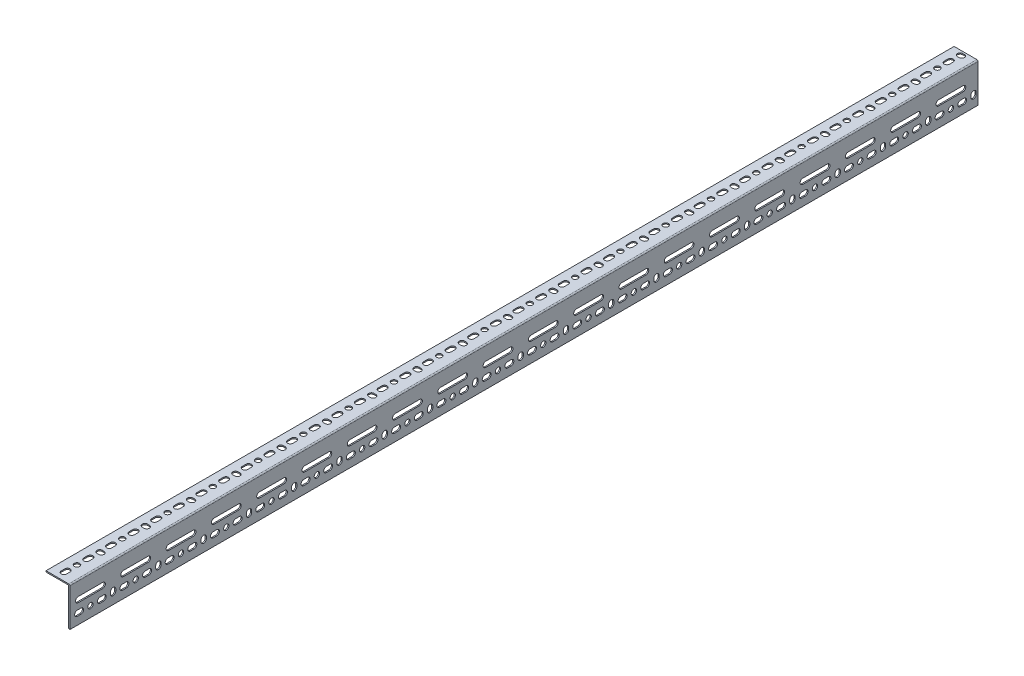
SolidWorks part; units mm, degrees
material "Black Iron Steel"
ref_plane "Front Plane" through (0, 0, 0) normal (0, 0, 1) x (1, 0, 0)
ref_plane "Top Plane" through (0, 0, 0) normal (0, 1, 0) x (1, 0, 0)
ref_plane "Right Plane" through (0, 0, 0) normal (1, 0, 0) x (0, 0, -1)
other "total length"
sketch "Sketch1" plane through (0, 0, 0) normal (0, 1, 0) x (1, 0, 0)
  line L0 (0, 0) -> (0, 1524)
  dimension "D1" = 1524
other "Structural Member1"
ref_plane "Plane1" through (0, 0, 0) normal (0, 0, 1) x (-1, 0, 0)
sketch "Sketch11" plane through (0, 0, 0) normal (0, 0, 1) x (-1, 0, 0)
  line L0 (0, 2) -> (0, 65.5)
  line L1 (0, 65.5) -> (1, 65.5)
  line L2 (2, 64.5) -> (2, 4)
  line L3 (4, 2) -> (39.1, 2)
  line L4 (40.1, 1) -> (40.1, 0)
  line L5 (40.1, 0) -> (2, 0)
  arc A0 (40.1, 1) -> (39.1, 2) centre (39.1, 1) ccw
  arc A1 (1, 65.5) -> (2, 64.5) centre (1, 64.5) cw
  arc A2 (4, 2) -> (2, 4) centre (4, 4) cw
  arc A3 (0, 2) -> (2, 0) centre (2, 2) ccw
  point P10 (21.05, 0)
  point P14 (0, 33.75)
  point P15 (2, 33.75)
  point P16 (21.05, 2)
  point P17 (2, 65.5)
  point P18 (40.1, 2)
  point P21 (0, 0)
  point P22 (0, 0)
  dimension "Radius_1" = 2
  dimension "D4" = 2
  dimension "D1" = 2
  dimension "H_leg" = 40.1
  dimension "D2" = 1
  dimension "D3" = 65.5
sketch "Sketch12" plane through (0, 0, 0) normal (0, 1, 0) x (1, 0, 0)
  line L0 (-22.6, 12.5) -> (-22.6, 18.5) construction
  line L1 (-27.1, 12.5) -> (-27.1, 18.5)
  line L2 (-18.1, 12.5) -> (-18.1, 18.5)
  line L3 (-40.1, 1524) -> (-40.1, 0) construction
  line L5 (-2, 0) -> (-40.1, 0) construction
  arc A0 (-27.1, 12.5) -> (-18.1, 12.5) centre (-22.6, 12.5) ccw
  arc A1 (-18.1, 18.5) -> (-27.1, 18.5) centre (-22.6, 18.5) ccw
  point P2 (-22.6, 15.5)
  dimension "D1" = 15
  dimension "D4" = 8
  dimension "D2" = 9
  dimension "D3" = 13
extrude "Slot 1.5" cut sketch "Sketch12" against normal through all
sketch "Sketch13" plane through (0, 0, 0) normal (0, 1, 0) x (1, 0, 0)
  line L0 (-22.6, 34.5) -> (-22.6, 15.5) construction
  circle A0 centre (-22.6, 34.5) radius 4.5
  arc A2 (-18.1, 18.5) -> (-27.1, 18.5) centre (-22.6, 18.5) ccw construction
  dimension "D1" = 7
  dimension "D2" = 9
extrude "Hole 1.5" cut sketch "Sketch13" against normal through all
sketch "Sketch18" plane through (0, 0, 0) normal (0, 1, 0) x (1, 0, 0)
  line L0 (-22.6, 72.5) -> (-19.6, 72.5) construction
  line L1 (-22.6, 77) -> (-19.6, 77)
  line L2 (-22.6, 68) -> (-19.6, 68)
  arc A0 (-22.6, 77) -> (-22.6, 68) centre (-22.6, 72.5) ccw
  arc A1 (-19.6, 68) -> (-19.6, 77) centre (-19.6, 72.5) ccw
  point P2 (-21.1, 72.5)
  dimension "D2" = 12
  dimension "D1" = 9
  dimension "D3" = 38
extrude "Vertical Slot 1.5" cut sketch "Sketch18" against normal through all
sketch "Sketch15" plane through (0, 0, 0) normal (1, 0, 0) x (0, 0, -1)
  line L0 (12.5, -48) -> (18.5, -48) construction
  line L1 (12.5, -43.5) -> (18.5, -43.5)
  line L2 (12.5, -52.5) -> (18.5, -52.5)
  line L6 (0, -65.5) -> (0, -2) construction
  line L7 (1524, -65.5) -> (0, -65.5) construction
  arc A0 (12.5, -43.5) -> (12.5, -52.5) centre (12.5, -48) ccw
  arc A1 (18.5, -52.5) -> (18.5, -43.5) centre (18.5, -48) ccw
  point P2 (15.5, -48)
  dimension "D1" = 15
  dimension "D3" = 8
  dimension "D2" = 9
  dimension "D4" = 13
extrude "Small Slot 2.5" cut sketch "Sketch15" against normal through all
sketch "Sketch16" plane through (0, 0, 0) normal (1, 0, 0) x (0, 0, -1)
  line L0 (34.5, -48) -> (15.5, -48) construction
  circle A0 centre (34.5, -48) radius 4.5
  arc A2 (18.5, -52.5) -> (18.5, -43.5) centre (18.5, -48) ccw construction
  dimension "D1" = 9
  dimension "D2" = 7
extrude "Hole 2.5" cut sketch "Sketch16" against normal through all
sketch "Sketch17" plane through (0, 0, 0) normal (1, 0, 0) x (0, 0, -1)
  line L0 (72.5, -45) -> (72.5, -48) construction
  line L1 (77, -45) -> (77, -48)
  line L2 (68, -45) -> (68, -48)
  line L3 (72.5, -48) -> (34.5, -48) construction
  arc A0 (77, -45) -> (68, -45) centre (72.5, -45) ccw
  arc A1 (68, -48) -> (77, -48) centre (72.5, -48) ccw
  point P2 (72.5, -46.5)
  dimension "D1" = 12
  dimension "D2" = 9
  dimension "D3" = 38
extrude "Vertical Slot 2.5" cut sketch "Sketch17" against normal through all
sketch "Sketch14" plane through (0, 0, 0) normal (1, 0, 0) x (0, 0, -1)
  line L0 (14, -28.95) -> (55, -28.95) construction
  line L1 (14, -24.45) -> (55, -24.45)
  line L2 (14, -33.45) -> (55, -33.45)
  line L8 (34.5, -48) -> (34.5, -28.95) construction
  arc A0 (14, -24.45) -> (14, -33.45) centre (14, -28.95) ccw
  arc A1 (55, -33.45) -> (55, -24.45) centre (55, -28.95) ccw
  point P2 (34.5, -28.95)
  dimension "D1" = 50
  dimension "D3" = 19.05
  dimension "D2" = 9
extrude "Long Slot 2.5" cut sketch "Sketch14" against normal through all
pattern_linear "Short Slot pattern 1.5" count 40 spacing 38 along (0, 0, -1) of "Slot 1.5", "Small Slot 2.5"
pattern_linear "Hole pattern" count 20 spacing 76 along (0, 0, -1) of "Hole 2.5", "Hole 1.5"
pattern_linear "Vert Slot Pattern" count 20 spacing 76 along (0, 0, -1) of "Vertical Slot 1.5", "Vertical Slot 2.5"
pattern_linear "Long Slot pattern" count 20 spacing 76 along (0, 0, -1) of "Long Slot 2.5"
equation "\"D4@Sketch11\" = \"Radius_1@Sketch11\""
